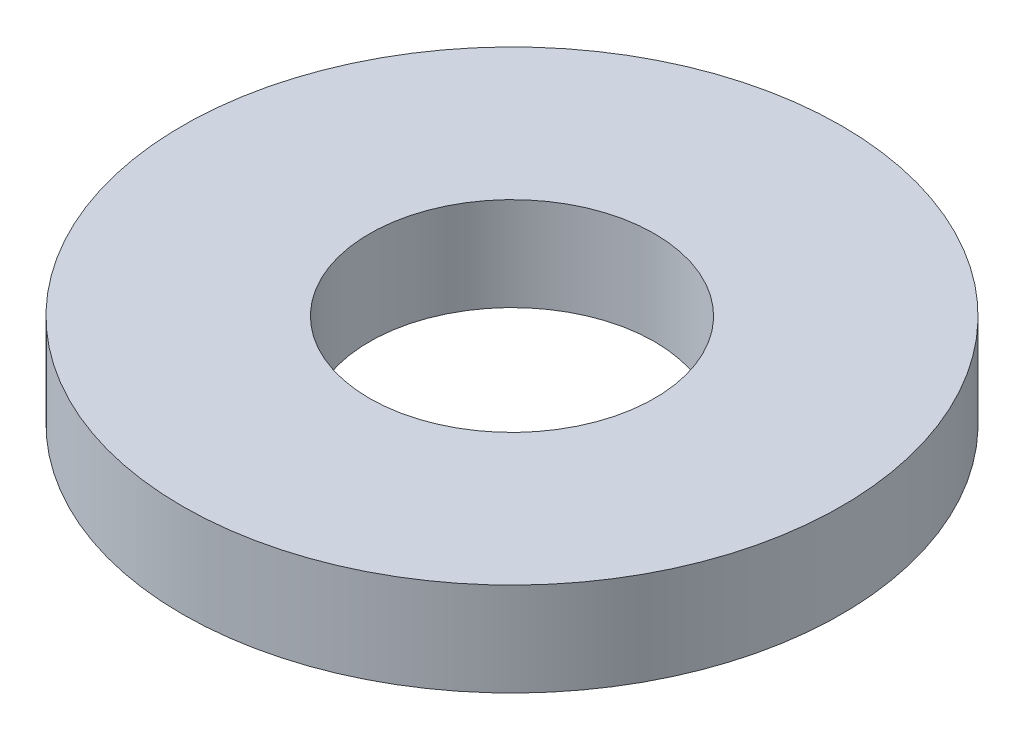
SolidWorks part; units mm, degrees
material "6061 合金"
ref_plane "前视基准面" through (0, 0, 0) normal (0, 0, 1) x (1, 0, 0)
ref_plane "上视基准面" through (0, 0, 0) normal (0, 1, 0) x (1, 0, 0)
ref_plane "右视基准面" through (0, 0, 0) normal (1, 0, 0) x (0, 0, -1)
other "Configuration Table"
sketch "草图1" plane through (0, 0, 0) normal (0, 1, 0) x (1, 0, 0)
  circle A0 centre (0, 0) radius 3.525
  circle A1 centre (0, 0) radius 1.525
  dimension "D1" = 3.05
  dimension "D2" = 2
extrude "凸台-拉伸1" add sketch "草图1" along normal blind 1
